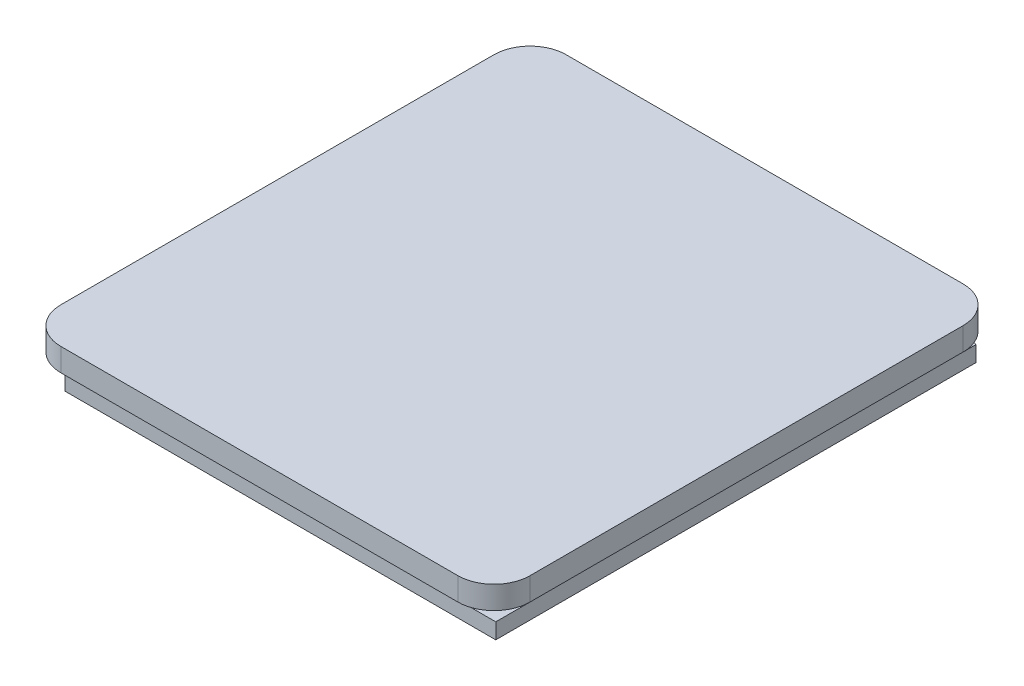
SolidWorks part; units mm, degrees
ref_plane "Front Plane" through (0, 0, 0) normal (0, 0, 1) x (1, 0, 0)
ref_plane "Top Plane" through (0, 0, 0) normal (0, 1, 0) x (1, 0, 0)
ref_plane "Right Plane" through (0, 0, 0) normal (1, 0, 0) x (0, 0, -1)
sketch "Sketch2" plane through (0, 0, 0) normal (0, 1, 0) x (1, 0, 0)
  line L1 (-16.5, -21) -> (16.5, -21)
  line L2 (-19.5, -18) -> (-19.5, 18)
  line L3 (-16.5, 21) -> (16.5, 21)
  line L4 (19.5, -18) -> (19.5, 18)
  line L5 (-19.5, -21) -> (19.5, 21) construction
  line L6 (-19.5, 21) -> (19.5, -21) construction
  arc A0 (-16.5, -21) -> (-19.5, -18) centre (-16.5, -18) cw
  arc A1 (16.5, -21) -> (19.5, -18) centre (16.5, -18) ccw
  arc A2 (16.5, 21) -> (19.5, 18) centre (16.5, 18) cw
  arc A3 (-19.5, 18) -> (-16.5, 21) centre (-16.5, 18) cw
  point P0 (0, 0)
  dimension "D3" = 3
  dimension "D1" = 42
  dimension "D2" = 39
extrude "Boss-Extrude1" add sketch "Sketch2" along normal blind 4.8
sketch "Sketch3" plane through (0, 0, 21) normal (0, 0, 1) x (1, 0, 0)
  line L0 (0, 0) -> (-19.5, 0) construction
  line L1 (-19.5, 0) -> (-17.9, 0) construction
  line L2 (-17.9, 0) -> (-17.9, 1.3) construction
  line L3 (-19.5, 4.8) -> (-19.5, 0) construction
  line L4 (0, 0) -> (0, 2.1316)
  line L6 (16.2, 2.9) -> (16.2, 1.3)
  line L7 (-17.9, 2.9) -> (-19.5, 2.9)
  line L8 (-19.5, 1.3) -> (-19.5, 2.9)
  line L9 (17.9, 0) -> (17.9, 1.3) construction
  line L10 (19.5, 1.3) -> (19.5, 2.9)
  line L11 (17.9, 2.9) -> (19.5, 2.9)
  line L14 (17.9, 1.3) -> (16.2, 1.3)
  line L15 (-17.9, 2.9) -> (-16.2, 2.9)
  line L16 (17.9, 2.9) -> (16.2, 2.9)
  line L17 (-17.9, 1.3) -> (-16.2, 1.3)
  line L18 (-16.2, 2.9) -> (-16.2, 1.3)
  line L20 (-17.9, 1.3) -> (-17.9, 0)
  line L21 (-17.9, 0) -> (-19.5, 0)
  line L22 (-19.5, 1.3) -> (-19.5, 0)
  line L24 (19.5, 1.3) -> (19.5, 0)
  line L25 (19.5, 0) -> (17.9, 0)
  line L26 (17.9, 1.3) -> (17.9, 0)
  dimension "D1" = 1.6
extrude "Cut-Extrude1" cut sketch "Sketch3" against normal blind 114.8
sketch "Sketch4" plane through (-19.5, 0, 0) normal (-1, 0, 0) x (0, 0, 1)
  line L1 (21, 0) -> (21, 1.2) construction
  line L2 (21, 4.8) -> (21, 2.9) construction
  line L3 (18, 2.9) -> (17.5, 2.9) construction
  line L4 (-18, 2.9) -> (18, 2.9) construction
  line L6 (17.5, 2.9) -> (21, 2.9)
  line L7 (17.5, 2.9) -> (17.5, 1.3)
  line L8 (17.5, 1.3) -> (19.25, 1.3)
  line L9 (21, 2.9) -> (21, 1.2)
  line L12 (19.25, 1.3) -> (19.25, 0)
  line L13 (19.25, 0) -> (21, 0)
  line L14 (21, 1.2) -> (21, 0)
extrude "Cut-Extrude2" cut sketch "Sketch4" against normal blind 114.8
